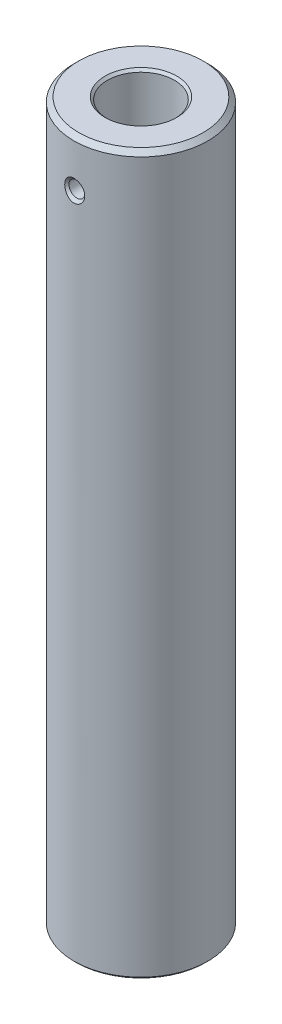
SolidWorks part; units mm, degrees
ref_plane "Plan de face" through (0, 0, 0) normal (0, 0, 1) x (1, 0, 0)
ref_plane "Plan de dessus" through (0, 0, 0) normal (0, 1, 0) x (1, 0, 0)
ref_plane "Plan de droite" through (0, 0, 0) normal (1, 0, 0) x (0, 0, -1)
sketch "Esquisse1" plane through (0, 0, 0) normal (0, 1, 0) x (1, 0, 0)
  circle A0 centre (0, 0) radius 14
extrude "Boss.-Extru.1" add sketch "Esquisse1" along normal blind 150
chamfer "Chanfrein1" distance 1 angle 45 1 edges at (0, 150, 14)
sketch "Esquisse2" plane through (0, 150, 0) normal (0, 1, 0) x (-1, 0, 0)
  point P0 (0, 0)
hole_wizard "Diamètre du perçage Ø14.0 (14)1" positions "Esquisse5" profile "Esquisse4" hole size "Ø14.0" standard "ISO"
sketch "Esquisse5" plane through (0, 150, 0) normal (0, 1, 0) x (-1, 0, 0)
  point P0 (0, 0)
sketch "Esquisse4" plane through (0, 150, 0) normal (1, 0, 0) x (0, 0, 1)
  line L0 (0, 0) -> (0, 39.206)
  line L1 (0, 39.206) -> (7, 35)
  line L2 (7, 35) -> (7, 0.5)
  line L3 (7, 0.5) -> (7.5, 0)
  line L5 (7.5, 0) -> (0, 0)
  line L6 (-7, 0.5) -> (-7.5, 0) construction
  line L10 (0, 39.206) -> (-7, 35) construction
  line L11 (0, -6.35) -> (0, 107.95) construction
  dimension "Diamètre du perçage" = 14
  dimension "Profondeur du perçage" = 35
  dimension "Diamètre du fraisage entrant" = 15
  dimension "Angle du fraisage entrant" = 90
  dimension "Angle de pointe" = 118
chamfer "Chanfrein2" distance 0.5 angle 45 1 edges at (0, 0, 14)
hole_wizard "Trou taraudé M8x1.01" positions "Esquisse7" profile "Esquisse6" tap size "M8x1.0" standard "ISO"
sketch "Esquisse7" plane through (0, 0, 0) normal (0, -1, 0) x (1, 0, 0)
  point P0 (0, 0)
sketch "Esquisse6" plane through (0, 0, 0) normal (1, 0, 0) x (0, 0, -1)
  line L0 (0, 0) -> (0, 27.103)
  line L1 (0, 27.103) -> (3.5, 25)
  line L2 (3.5, 25) -> (3.5, 0)
  line L5 (3.5, 0) -> (0, 0)
  line L10 (0, 27.103) -> (-3.5, 25) construction
  line L11 (0, -6.35) -> (0, 107.95) construction
  dimension "Diamètre du trou pour taraudage" = 7
  dimension "Profondeur du trou pour taraudage" = 25
  dimension "Angle de pointe" = 118
cosmetic thread "Filetage de perçage1" parameters "D1"=20, "D2"=8
sketch "Esquisse8" plane through (0, 0, 0) normal (0, 0, 1) x (1, 0, 0)
  line L1 (0, 146.238) -> (0, 132.6328) construction
  line L2 (7.5, 140) -> (-7.5, 140)
  line L3 (7.5, 140) -> (-7.5, 140) construction
  point P5 (0, 140)
  dimension "D1" = 10
hole_wizard "Trou taraudé M42" positions "Esquisse12" profile "Esquisse11" tap size "M4" standard "ISO" end condition up to next
sketch "Esquisse12" plane through (0, 0, 0) normal (0, 0, 1) x (1, 0, 0)
  point P0 (0, 140)
sketch "Esquisse11" plane through (0, 140, 0) normal (1, 0, 0) x (0, 1, 0)
  line L0 (0, 0) -> (0, 14)
  line L1 (0, 14) -> (2.25, 14)
  line L2 (1.65, 13.4) -> (1.65, 0)
  line L5 (1.65, 0) -> (0, 0)
  line L7 (2.25, 14) -> (1.65, 13.4)
  line L8 (-2.25, 14) -> (-1.65, 13.4) construction
  line L11 (0, -6.35) -> (0, 107.95) construction
  dimension "Diamètre du trou pour taraudage jusqu'au prochain" = 3.3
  dimension "Profondeur du trou pour taraudage jusqu'au prochain" = 14
  dimension "Diamètre du fraisage débouchant" = 4.5
  dimension "Angle du fraisage débouchant" = 90
cosmetic thread "Filetage de perçage2" parameters "D2"=4
